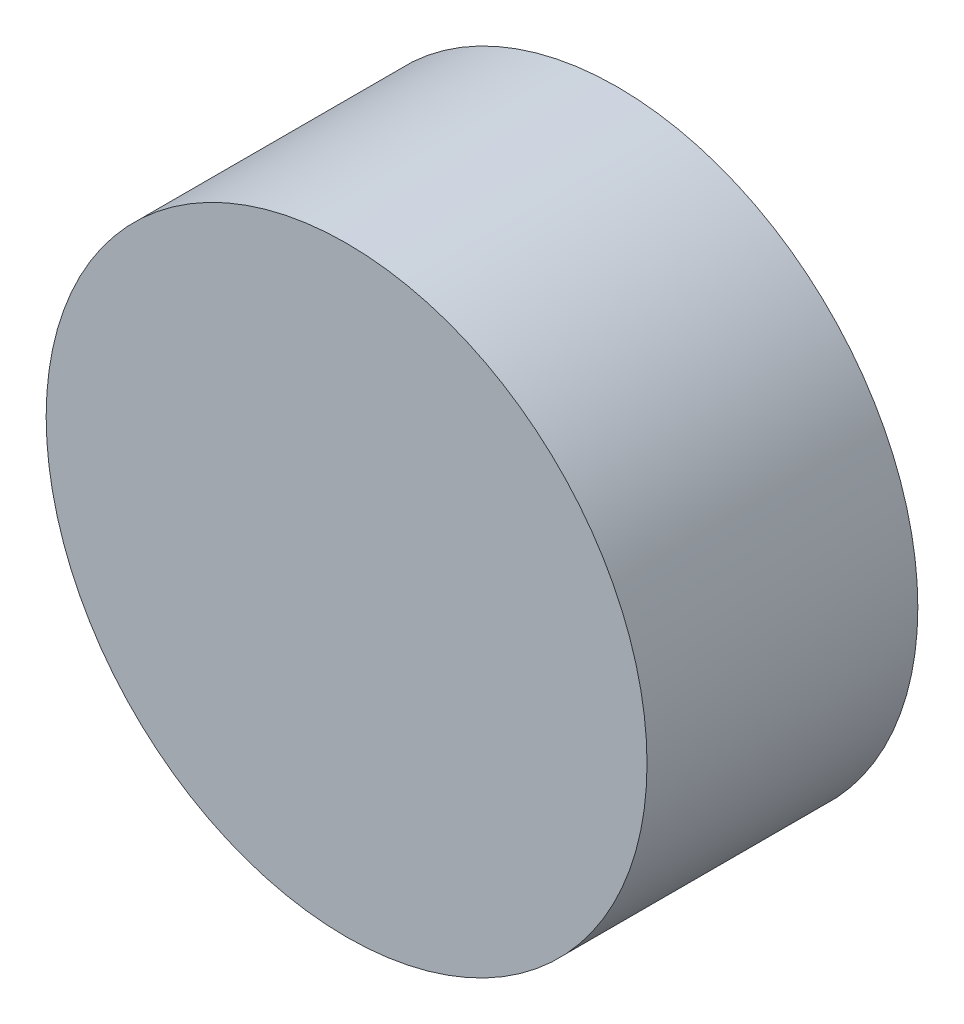
SolidWorks part; units mm, degrees
ref_plane "Plan de face" through (0, 0, 0) normal (0, 0, 1) x (1, 0, 0)
ref_plane "Plan de dessus" through (0, 0, 0) normal (0, 1, 0) x (1, 0, 0)
ref_plane "Plan de droite" through (0, 0, 0) normal (1, 0, 0) x (0, 0, -1)
sketch "Esquisse1" plane through (0, 0, 0) normal (0, 0, 1) x (1, 0, 0)
  circle A0 centre (0, 0) radius 35.5
extrude "Boss.-Extru.1" add sketch "Esquisse1" along normal blind 32
